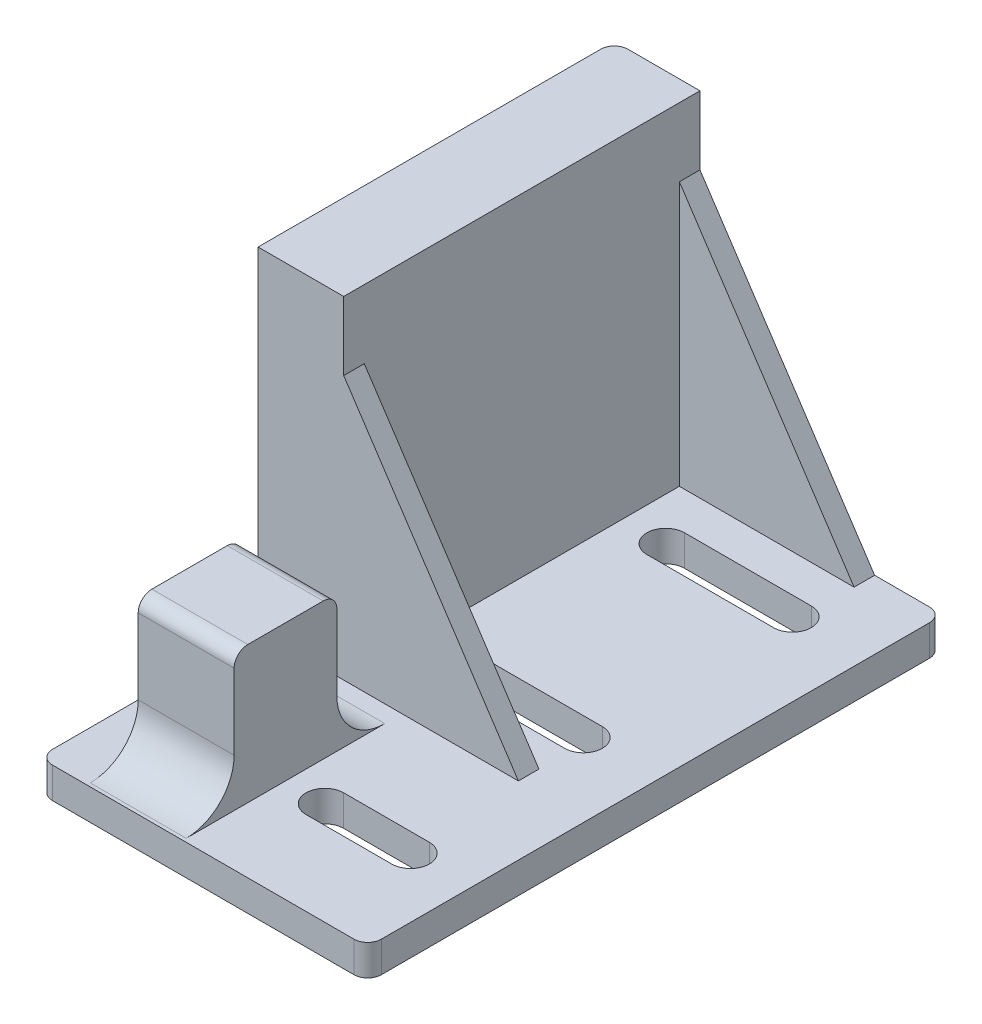
SolidWorks part; units mm, degrees
ref_plane "Front Plane" through (0, 0, 0) normal (0, 0, 1) x (1, 0, 0)
ref_plane "Top Plane" through (0, 0, 0) normal (0, 1, 0) x (1, 0, 0)
ref_plane "Right Plane" through (0, 0, 0) normal (1, 0, 0) x (0, 0, -1)
sketch "Sketch1" plane through (0, 0, 0) normal (0, 1, 0) x (1, 0, 0)
  line L0 (24, -42) -> (24, 42)
  line L1 (-24, -42) -> (24, -42)
  line L2 (-24, -42) -> (-24, 42)
  line L3 (-24, 42) -> (24, 42)
  dimension "D1" = 84
  dimension "D2" = 48
  dimension "D3" = 24
  dimension "D4" = 42
extrude "Boss-Extrude1" add sketch "Sketch1" along normal blind 4.5
fillet "Fillet1" radius 2 4 edges at (24, 2.25, -42) (-24, 2.25, -42) (24, 2.25, 42) (-24, 2.25, 42)
sketch "Sketch2" plane through (0, 4.5, 0) normal (0, 1, 0) x (1, 0, 0)
  line L0 (-40.7835, 15.5) -> (41.7164, 15.5) construction
  line L1 (-5.25, 33.5) -> (13.25, 33.5)
  line L3 (-5.25, 28) -> (13.25, 28)
  line L6 (-24, 40) -> (-24, -40) construction
  line L7 (22, 42) -> (-22, 42) construction
  line L8 (-5.25, 3) -> (13.25, 3)
  line L9 (-5.25, -2.5) -> (13.25, -2.5)
  arc A0 (-5.25, 33.5) -> (-5.25, 28) centre (-5.25, 30.75) ccw
  arc A1 (13.25, 28) -> (13.25, 33.5) centre (13.25, 30.75) ccw
  arc A2 (-5.25, -2.5) -> (-5.25, 3) centre (-5.25, 0.25) cw
  arc A3 (13.25, 3) -> (13.25, -2.5) centre (13.25, 0.25) cw
  dimension "D2" = 5.5
  dimension "D3" = 5.5
  dimension "D1" = 5.5
  dimension "D4" = 18.75
  dimension "D5" = 11.25
  dimension "D6" = 15.25
  dimension "D7" = 18.5
extrude "Cut-Extrude1" cut sketch "Sketch2" against normal through all
sketch "Sketch3" plane through (0, 4.5, 0) normal (0, 1, 0) x (1, 0, 0)
  line L0 (22, 42) -> (-22, 42) construction
  line L1 (-11.5, 42) -> (-22, 42)
  line L2 (-11.5, 42) -> (-11.5, -10)
  line L3 (-11.5, -10) -> (-24, -10)
  line L4 (-24, 40) -> (-24, -10)
  line L5 (-24, 40) -> (-24, -40) construction
  arc A2 (-22, 42) -> (-24, 40) centre (-22, 40) ccw
  arc A3 (-22, 42) -> (-24, 40) centre (-22, 40) ccw
  dimension "D1" = 50
  dimension "D2" = 12.5
  dimension "D3" = 0
extrude "Boss-Extrude2" add sketch "Sketch3" along normal blind 48.5
sketch "Sketch4" plane through (0, 0, -42) normal (0, 0, -1) x (-1, 0, 0)
  line L0 (-14, 4.5) -> (11.5, 43)
  line L1 (-22, 4.5) -> (11.5, 4.5) construction
  line L2 (11.5, 53) -> (11.5, 4.5) construction
  dimension "D1" = 10
  dimension "D2" = 10
rib "Rib1" sketch "Sketch4" sketch "Sketch4" thickness 3 extrusion direction parallel to sketch draft on no parameters "D1"=3
sketch "Sketch5" plane through (0, 0, 10) normal (0, 0, 1) x (1, 0, 0)
  line L0 (14, 4.5) -> (-11.5, 43)
  line L1 (-22, 4.5) -> (22, 4.5) construction
  line L2 (14, 4.5) -> (-11.5, 43) construction
rib "Rib14" sketch "Sketch5" sketch "Sketch5" thickness 3 extrusion direction parallel to sketch draft on no parameters "D1"=3
sketch "Sketch6" plane through (-24, 0, 0) normal (-1, 0, 0) x (0, 0, 1)
  line L0 (-40, 53) -> (10, 53) construction
  line L1 (10, 53) -> (10, 4.5) construction
  circle A0 centre (-16, 25.65) radius 11.1
  dimension "D1" = 22.2
  dimension "D2" = 27.35
  dimension "D3" = 26
extrude "Cut-Extrude2" cut sketch "Sketch6" against normal blind 8
sketch "Sketch7" plane through (0, 4.5, 0) normal (0, 1, 0) x (1, 0, 0)
  line L0 (-22, -42) -> (22, -42) construction
  line L1 (-17, -19.5) -> (-3, -19.5)
  line L2 (-17, -19.5) -> (-17, -34.5)
  line L3 (-17, -34.5) -> (-3, -34.5)
  line L4 (-3, -19.5) -> (-3, -34.5)
  line L5 (-24, -10) -> (-24, -40) construction
  dimension "D1" = 14
  dimension "D2" = 15
  dimension "D3" = 7.5
  dimension "D4" = 7
extrude "Boss-Extrude3" add sketch "Sketch7" along normal blind 20
fillet "Fillet2" radius 7 2 edges at (-10, 4.5, 34.5) (-10, 4.5, 19.5)
fillet "Fillet3" radius 2 2 edges at (-10, 24.5, 34.5) (-10, 24.5, 19.5)
sketch "Sketch8" plane through (-17, 0, 0) normal (-1, 0, 0) x (0, 0, 1)
  line L0 (21.5, 24.5) -> (32.5, 24.5) construction
  line L1 (34.5, 22.5) -> (34.5, 11.5) construction
  circle A0 centre (27, 16.5) radius 4
  dimension "D1" = 8
  dimension "D2" = 8
  dimension "D3" = 7.5
extrude "Cut-Extrude3" cut sketch "Sketch8" against normal blind 10 contours A0
sketch "Sketch9" plane through (0, 4.5, 0) normal (0, 1, 0) x (1, 0, 0)
  line L1 (2.75, -24.25) -> (15.25, -24.25)
  line L3 (2.75, -29.75) -> (15.25, -29.75)
  line L5 (24, -40) -> (24, 40) construction
  line L6 (-3, -21.5) -> (-17, -21.5) construction
  arc A0 (2.75, -24.25) -> (2.75, -29.75) centre (2.75, -27) ccw
  arc A1 (15.25, -29.75) -> (15.25, -24.25) centre (15.25, -27) ccw
  dimension "D4" = 2.75
  dimension "D5" = 2.75
  dimension "D6" = 2.75
  dimension "D1" = 12.5
  dimension "D2" = 5.5
  dimension "D3" = 8.75
extrude "Cut-Extrude4" cut sketch "Sketch9" against normal through all
